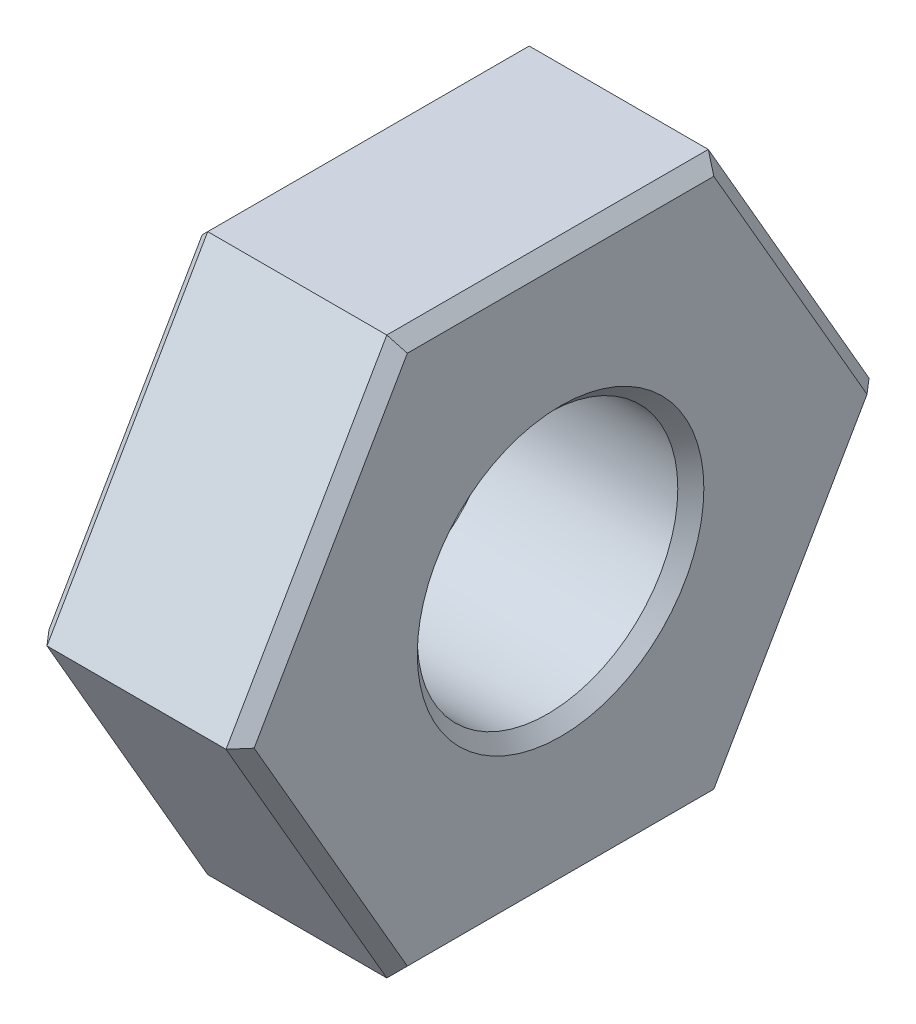
SolidWorks part; units mm, degrees
ref_plane "Front Plane" through (0, 0, 0) normal (0, 0, 1) x (1, 0, 0)
ref_plane "Top Plane" through (0, 0, 0) normal (0, 1, 0) x (1, 0, 0)
ref_plane "Right Plane" through (0, 0, 0) normal (1, 0, 0) x (0, 0, -1)
sketch "Sketch2" plane through (0, 0, 0) normal (1, 0, 0) x (0, 0, -1)
  line L1 (4.9363, 0) -> (2.4682, 4.275)
  line L2 (2.4682, 4.275) -> (-2.4682, 4.275)
  line L3 (-2.4682, 4.275) -> (-4.9363, 0)
  line L4 (-4.9363, 0) -> (-2.4682, -4.275)
  line L5 (-2.4682, -4.275) -> (2.4682, -4.275)
  line L6 (2.4682, -4.275) -> (4.9363, 0)
  circle A0 centre (0, 0) radius 4.275 construction
extrude "Boss-Extrude3" add sketch "Sketch2" along normal blind 3.15
sketch "Sketch3" plane through (3.15, 0, 0) normal (1, 0, 0) x (0, 0, -1)
  circle A0 centre (0, 0) radius 2
extrude "Cut-Extrude2" cut sketch "Sketch3" against normal blind 7
chamfer "Chamfer1" distance 0.2 angle 45 14 edges at (0, 2.1375, -3.7023) (0, 4.275, 0) (0, 2.1375, 3.7023) (0, -2.1375, 3.7023) (0, -4.275, 0) (0, -2.1375, -3.7023) (0, 0, -2) (3.15, -4.275, 0) (3.15, -2.1375, 3.7023) (3.15, 2.1375, 3.7023) (3.15, 4.275, 0) (3.15, 2.1375, -3.7023) (3.15, -2.1375, -3.7023) (3.15, 0, -2)
